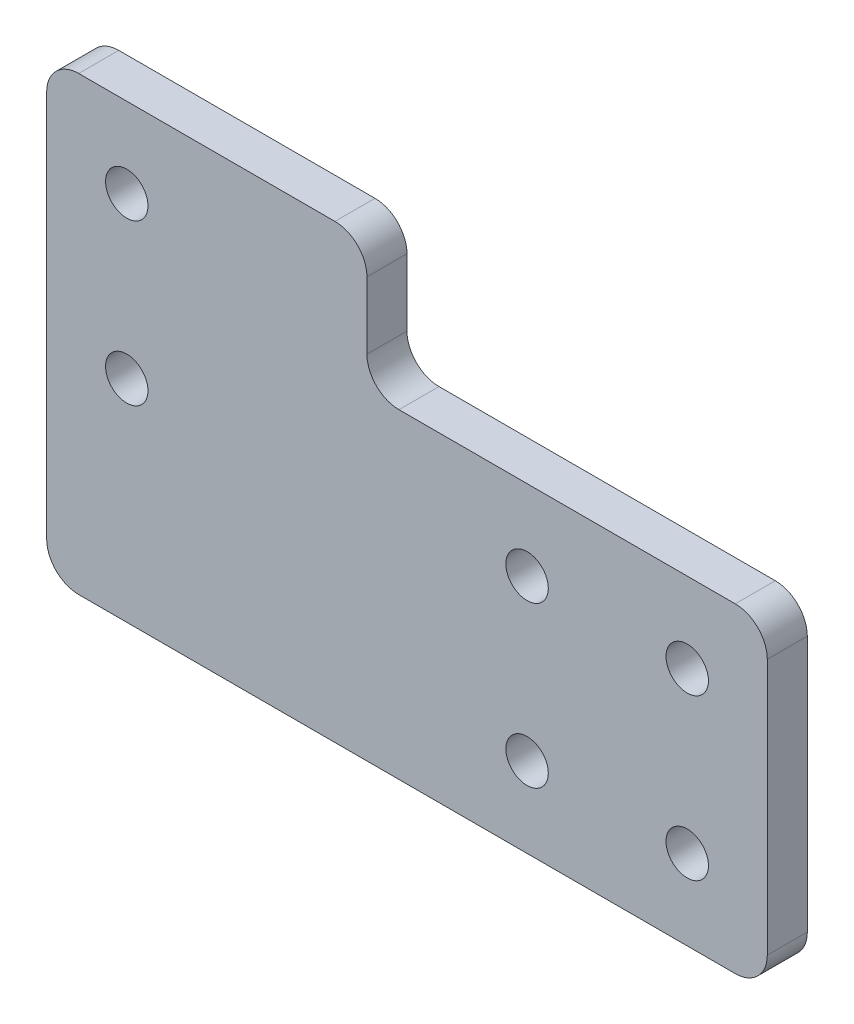
SolidWorks part; units mm, degrees
ref_plane "Front Face Plane" through (0, 0, 0) normal (0, 0, 1) x (1, 0, 0)
ref_plane "Top Plane" through (0, 0, 0) normal (0, 1, 0) x (1, 0, 0)
ref_plane "Right Plane" through (0, 0, 0) normal (1, 0, 0) x (0, 0, -1)
ref_plane "Back Face Plane" through (0, 0, 5) normal (0, 0, 1) x (1, 0, 0)
sketch "End Cap Sketch" plane through (0, 0, 0) normal (0, 0, 1) x (1, 0, 0)
  line L0 (-66, -20) -> (16, -20)
  line L1 (20, -16) -> (20, 16)
  line L2 (16, 20) -> (-26, 20)
  line L4 (-30, 24) -> (-30, 32.365)
  line L5 (-34, 36.365) -> (-66, 36.365)
  line L6 (-70, 32.365) -> (-70, -16)
  line L7 (20, 0) -> (-70, 0) construction
  circle A0 centre (-10, 10) radius 2.65
  circle A1 centre (-10, -10) radius 2.65
  circle A2 centre (10, 10) radius 2.65
  circle A3 centre (10, -10) radius 2.65
  circle A4 centre (-60, 26.365) radius 2.65
  circle A5 centre (-60, 6.365) radius 2.65
  arc A6 (-26, 20) -> (-30, 24) centre (-26, 24) cw
  arc A7 (-30, 32.365) -> (-34, 36.365) centre (-34, 32.365) ccw
  arc A8 (-66, 36.365) -> (-70, 32.365) centre (-66, 32.365) ccw
  arc A9 (-70, -16) -> (-66, -20) centre (-66, -16) ccw
  arc A10 (16, -20) -> (20, -16) centre (16, -16) ccw
  arc A11 (20, 16) -> (16, 20) centre (16, 16) ccw
  point P31 (-30, 36.365)
  point P37 (-70, 36.365)
  point P42 (20, -20)
  point P45 (20, 20)
  dimension "D2" = 5.3
  dimension "D7" = 50
  dimension "D12" = 10
  dimension "D19" = 4
  dimension "D1" = 40
  dimension "D3" = 10
  dimension "D4" = 10
  dimension "D5" = 10
  dimension "D6" = 10
  dimension "D8" = 20
  dimension "D9" = 20
  dimension "D10" = 20
  dimension "D11" = 30
  dimension "D18" = 6.365
extrude "Extrude Thickness" add sketch "End Cap Sketch" along normal blind 5
equation "\"Pulley Y Position\"= 38mm"
